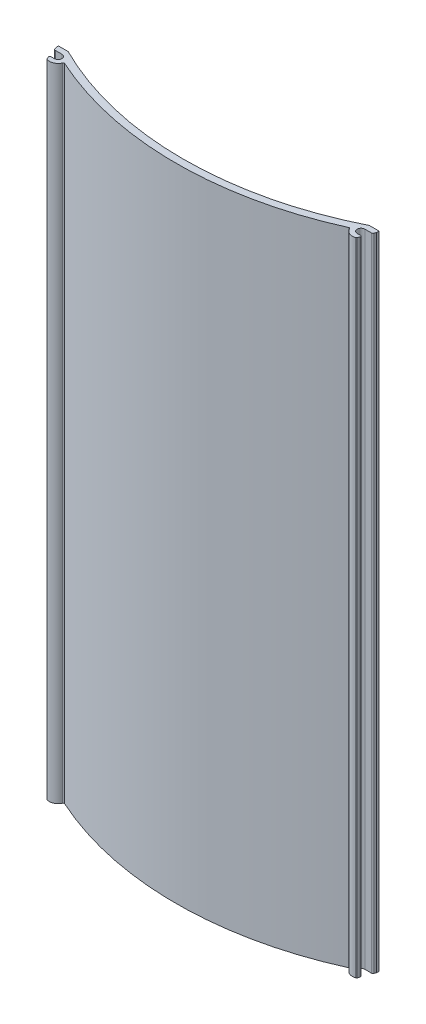
SolidWorks part; units mm, degrees
material "6463-T6"
ref_plane "Front Plane" through (0, 0, 0) normal (0, 0, 1) x (1, 0, 0)
ref_plane "Top Plane" through (0, 0, 0) normal (0, 1, 0) x (1, 0, 0)
ref_plane "Right Plane" through (0, 0, 0) normal (1, 0, 0) x (0, 0, -1)
sketch "Sketch1" plane through (0, 0, 0) normal (0, 1, 0) x (1, 0, 0)
  line L0 (0, 6.3541) -> (101.5848, 6.3541) construction
  line L1 (0, 0) -> (101.5848, 0) construction
  line L2 (0, 0) -> (0, 25.4) construction
  line L3 (0, 25.4) -> (101.5848, 25.4) construction
  line L4 (101.5848, 0) -> (101.5848, 25.4) construction
  line L5 (0, 12.7) -> (101.5848, 12.7) construction
  line L6 (0, 19.05) -> (101.5848, 19.05) construction
  line L7 (50.7924, 25.4) -> (50.7924, 0) construction
  line L8 (12.7, 25.4) -> (12.7, 0) construction
  line L9 (76.1924, 25.4) -> (76.1924, 0) construction
  line L10 (25.4, 25.4) -> (25.4, 0) construction
  line L11 (38.1, 25.4) -> (38.1, 0) construction
  line L12 (63.4924, 25.4) -> (63.4924, 0) construction
  line L13 (88.8924, 25.4) -> (88.8924, 0) construction
  line L15 (101.5848, 6.3541) -> (101.5848, 4.3221)
  line L16 (100.0608, 5.4351) -> (100.0608, 4.3221)
  line L17 (100.5688, 3.8141) -> (101.0768, 3.8141)
  line L19 (0, 0) -> (-3.2676, 0) construction
  line L20 (1.3386, 5.3381) -> (0, 5.3381)
  line L26 (90.0621, 10.016) -> (95.6249, 0.381)
  line L27 (95.6249, 0.381) -> (95.6249, 0)
  line L28 (95.6249, 0) -> (97.1489, 0)
  line L29 (97.1489, 0) -> (97.1489, 0.381)
  line L30 (97.1489, 0.381) -> (112.7608, 0.381)
  line L31 (112.7608, 0.381) -> (112.7608, 0)
  line L32 (112.7608, 0) -> (114.2848, 0)
  line L33 (114.2848, 0) -> (114.2848, 1.905)
  line L34 (114.2848, 1.905) -> (96.5048, 1.905)
  line L35 (96.5048, 1.905) -> (92.3687, 9.0689)
  line L36 (97.1489, 0.381) -> (95.6249, 0.381) construction
  line L38 (0, 5.3381) -> (0, 6.3541)
  line L39 (101.5848, 5.3381) -> (100.8228, 3.8141)
  arc A0 (101.5848, 6.3541) -> (0, 6.3541) centre (50.7924, -88.9) ccw
  arc A1 (100.0608, 5.4351) -> (1.3386, 5.3381) centre (50.7924, -88.9) ccw
  circle A2 centre (50.7924, -88.9) radius 107.95 construction
  circle A3 centre (50.7924, -88.9) radius 106.426 construction
  arc A4 (100.0608, 4.3221) -> (100.5688, 3.8141) centre (100.5688, 4.3221) ccw
  arc A5 (101.0768, 3.8141) -> (101.5848, 4.3221) centre (101.0768, 4.3221) ccw
  point P33 (100.0608, 3.8141)
  point P38 (101.5848, 3.8141)
  dimension "D12" = 2.54
  dimension "D14" = 0.508
  dimension "D16" = 107.95
  dimension "D1" = 101.5848
  dimension "D2" = 25.4
  dimension "D3" = 12.7
  dimension "D4" = 12.7
  dimension "D5" = 12.7
  dimension "D6" = 12.7
  dimension "D7" = 12.7
  dimension "D8" = 12.7
  dimension "D9" = 1.016
  dimension "D10" = 6.35
  dimension "D13" = 1.524
  dimension "D15" = 1.016
  dimension "D20" = 0.762
  dimension "D21" = 1.524
  dimension "D22" = 1.524
  dimension "D23" = 1.524
  dimension "D24" = 12.7
  dimension "D25" = 5.08
  dimension "D26" = 60
  dimension "D27" = 1.524
  dimension "D11" = 1.524
extrude "Boss-Extrude1" add sketch "Sketch1" along normal blind 203.2
sketch "Sketch3" plane through (0, 203.2, 0) normal (0, 1, 0) x (1, 0, 0)
  line L1 (101.5848, 6.3541) -> (101.5848, 5.3381) construction
  line L2 (100.0608, 2.9237) -> (101.5848, 2.9237)
  line L3 (101.5848, 2.9237) -> (101.5848, 5.5921)
  line L4 (101.5848, 5.5921) -> (100.0608, 5.4351)
  line L5 (100.0608, 5.4351) -> (100.0608, 2.9237)
  line L6 (0, 5.5921) -> (0.4068, 4.4744)
  line L7 (0, 5.3381) -> (0, 6.3541) construction
  line L8 (0.4068, 4.4744) -> (0, 4.4744)
  line L9 (0, 4.4744) -> (0, 5.5921)
  dimension "D1" = 0.762
  dimension "D2" = 0.762
  dimension "D3" = 2.6684
  dimension "D4" = 20
  dimension "D5" = 1.1176
extrude "Cut-Extrude1" cut sketch "Sketch3" against normal through all
sketch "Sketch2" plane through (0, 203.2, 0) normal (0, 1, 0) x (1, 0, 0)
  line L1 (101.5848, 6.3541) -> (101.5848, 5.5921) construction
  line L2 (101.2381, 4.6396) -> (101.5848, 5.5921)
  line L3 (101.2381, 4.6396) -> (98.7908, 4.6396)
  line L4 (98.7908, 2.2266) -> (99.8157, 2.2266)
  line L5 (100.1737, 1.7153) -> (99.9473, 1.0931)
  line L9 (50.7924, -88.9) -> (50.7924, 34.1205) construction
  line L10 (1.411, 1.7153) -> (1.6375, 1.0931)
  line L15 (2.794, 2.2266) -> (1.7691, 2.2266)
  line L16 (101.5848, 5.5921) -> (100.0608, 5.4351) construction
  line L19 (0.3467, 4.6396) -> (2.794, 4.6396)
  line L20 (0.3467, 4.6396) -> (0.0924, 5.3381)
  line L22 (101.5848, 5.5921) -> (100.0608, 5.4351)
  line L23 (1.3386, 5.3381) -> (0.0924, 5.3381) construction
  line L24 (1.3386, 5.3381) -> (0.0924, 5.3381)
  arc A0 (100.0608, 5.4351) -> (98.6476, 6.1598) centre (50.7924, -88.9) ccw
  arc A2 (98.7908, 2.2266) -> (98.7908, 4.6396) centre (98.7908, 3.4331) cw
  arc A3 (99.7187, 0.8651) -> (98.6476, 6.1598) centre (98.7908, 3.4331) cw
  arc A4 (99.8157, 2.2266) -> (100.1737, 1.7153) centre (99.8157, 1.8456) cw
  arc A5 (99.9473, 1.0931) -> (99.7187, 0.8651) centre (99.5892, 1.2234) cw
  arc A13 (1.6375, 1.0931) -> (1.866, 0.8651) centre (1.9955, 1.2234) ccw
  arc A14 (1.7691, 2.2266) -> (1.411, 1.7153) centre (1.7691, 1.8456) ccw
  arc A15 (1.866, 0.8651) -> (2.9371, 6.1598) centre (2.794, 3.4331) ccw
  arc A16 (2.794, 2.2266) -> (2.794, 4.6396) centre (2.794, 3.4331) ccw
  arc A17 (100.0608, 5.4351) -> (1.3386, 5.3381) centre (50.7924, -88.9) ccw construction
  arc A18 (2.9371, 6.1598) -> (1.3386, 5.3381) centre (50.7924, -88.9) ccw
  dimension "D2" = 2.413
  dimension "D3" = 5.461
  dimension "D4" = 0.381
  dimension "D12" = 20
  dimension "D6" = 2.794
  dimension "D5" = 0.9525
  dimension "D15" = 0.762
extrude "Boss-Extrude2" add sketch "Sketch2" against normal up to surface (203.2 mm away) up to face at (43.5213, 0, -9.2627)
fillet "Fillet1" radius 0.508 2 edges at (101.2381, 101.6, -4.6396) (0.3467, 101.6, -4.6396)
sketch "Sketch4" plane through (0, 203.2, 0) normal (0, 1, 0) x (1, 0, 0)
  line L10 (0, 5.5921) -> (0.225, 4.9738)
  line L11 (0.7024, 4.6396) -> (2.794, 4.6396)
  line L12 (2.794, 2.2266) -> (1.7691, 2.2266)
  line L13 (1.411, 1.7153) -> (1.6375, 1.0931)
  line L14 (99.9473, 1.0931) -> (100.1737, 1.7153)
  line L15 (99.8157, 2.2266) -> (98.7908, 2.2266)
  line L16 (98.7908, 4.6396) -> (100.8824, 4.6396)
  line L17 (101.3597, 4.9738) -> (101.5848, 5.5921)
  line L18 (101.5848, 5.5921) -> (101.5848, 6.3541)
  line L19 (0, 6.3541) -> (0, 5.5921)
  arc A0 (3.1857, 6.2846) -> (98.399, 6.2846) centre (50.7924, 101.753) ccw
  arc A1 (5.4194, 2.6829) -> (96.1653, 2.6829) centre (50.7924, 101.753) ccw
  arc A2 (98.6476, 6.1598) -> (99.7187, 0.8651) centre (98.7908, 3.4331) ccw construction
  arc A3 (98.6476, 6.1598) -> (2.9371, 6.1598) centre (50.7924, -88.9) ccw construction
  arc A4 (1.866, 0.8651) -> (2.9371, 6.1598) centre (2.794, 3.4331) ccw construction
  arc A5 (98.6476, 6.1598) -> (96.1653, 2.6829) centre (98.7908, 3.4331) ccw
  arc A6 (98.6476, 6.1598) -> (98.399, 6.2846) centre (50.7924, -88.9) ccw
  arc A7 (5.4194, 2.6829) -> (2.9371, 6.1598) centre (2.794, 3.4331) ccw
  arc A8 (3.1857, 6.2846) -> (2.9371, 6.1598) centre (50.7924, -88.9) ccw
  arc A14 (0.225, 4.9738) -> (0.7024, 4.6396) centre (0.7024, 5.1476) ccw
  arc A15 (2.794, 2.2266) -> (2.794, 4.6396) centre (2.794, 3.4331) ccw
  arc A16 (1.7691, 2.2266) -> (1.411, 1.7153) centre (1.7691, 1.8456) ccw
  arc A17 (1.6375, 1.0931) -> (1.866, 0.8651) centre (1.9955, 1.2234) ccw
  arc A18 (1.866, 0.8651) -> (2.9371, 6.1598) centre (2.794, 3.4331) ccw
  arc A20 (98.6476, 6.1598) -> (2.9371, 6.1598) centre (50.7924, -88.9) ccw
  arc A22 (98.6476, 6.1598) -> (99.7187, 0.8651) centre (98.7908, 3.4331) ccw
  arc A23 (99.7187, 0.8651) -> (99.9473, 1.0931) centre (99.5892, 1.2234) ccw
  arc A24 (100.1737, 1.7153) -> (99.8157, 2.2266) centre (99.8157, 1.8456) ccw
  arc A25 (98.7908, 4.6396) -> (98.7908, 2.2266) centre (98.7908, 3.4331) ccw
  arc A26 (100.8824, 4.6396) -> (101.3597, 4.9738) centre (100.8824, 5.1476) ccw
  arc A27 (101.5848, 6.3541) -> (0, 6.3541) centre (50.7924, -88.9) ccw
  arc A32 (5.4194, 2.6829) -> (3.9919, 5.8868) centre (2.794, 3.4331) ccw
  arc A36 (97.5929, 5.8868) -> (96.1653, 2.6829) centre (98.7908, 3.4331) ccw
  arc M35 (1.866, 0.8651) -> (2.9371, 6.1598) centre (2.794, 3.4331) ccw
  arc M37 (2.9371, 6.1598) -> (98.6476, 6.1598) centre (50.7924, -88.9) cw
  arc M39 (98.6476, 6.1598) -> (99.7187, 0.8651) centre (98.7908, 3.4331) ccw
  dimension "D2" = 213.36
  dimension "D3" = 108.966
  dimension "D1" = 0
extrude "Boss-Extrude3" add sketch "Sketch4" against normal through all contours A1 A0 M35 M39 | A0 M37 M35 | A0 M39 M37
sketch "Sketch5" plane through (0, 203.2, 0) normal (0, 1, 0) x (1, 0, 0)
  line L0 (101.5848, 6.3541) -> (98.5382, 6.3541)
  line L1 (3.0466, 6.3541) -> (0, 6.3541)
  line L10 (0, 5.5921) -> (0.225, 4.9738)
  line L11 (0.7024, 4.6396) -> (2.794, 4.6396)
  line L12 (2.794, 2.2266) -> (1.7691, 2.2266)
  line L13 (1.411, 1.7153) -> (1.6375, 1.0931)
  line L14 (99.9473, 1.0931) -> (100.1737, 1.7153)
  line L15 (99.8157, 2.2266) -> (98.7908, 2.2266)
  line L16 (98.7908, 4.6396) -> (100.8824, 4.6396)
  line L17 (101.3597, 4.9738) -> (101.5848, 5.5921)
  line L18 (101.5848, 5.5921) -> (101.5848, 6.3541)
  line L19 (0, 6.3541) -> (0, 5.5921)
  line L32 (99.9473, 1.0931) -> (100.1737, 1.7153)
  line L34 (99.8157, 2.2266) -> (98.7908, 2.2266)
  line L36 (98.7908, 4.6396) -> (100.8824, 4.6396)
  line L38 (101.3597, 4.9738) -> (101.5848, 5.5921)
  line L40 (101.5848, 5.5921) -> (101.5848, 6.3541)
  line L42 (0, 6.3541) -> (0, 5.5921)
  line L44 (0, 5.5921) -> (0.225, 4.9738)
  line L46 (0.7024, 4.6396) -> (2.794, 4.6396)
  line L48 (2.794, 2.2266) -> (1.7691, 2.2266)
  line L50 (1.411, 1.7153) -> (1.6375, 1.0931)
  arc A0 (98.399, 6.2846) -> (3.1857, 6.2846) centre (50.7924, -88.9) ccw construction
  arc A1 (3.1857, 6.2846) -> (98.399, 6.2846) centre (50.7924, 101.753) ccw construction
  arc A2 (98.399, 6.2846) -> (3.1857, 6.2846) centre (50.7924, -88.9) ccw
  arc A3 (3.0466, 6.3541) -> (3.1857, 6.2846) centre (50.7924, 101.753) ccw
  arc A4 (98.399, 6.2846) -> (98.5382, 6.3541) centre (50.7924, 101.753) ccw
  arc A6 (96.1653, 2.6829) -> (99.7187, 0.8651) centre (98.7908, 3.4331) ccw
  arc A7 (5.4194, 2.6829) -> (96.1653, 2.6829) centre (50.7924, 101.753) ccw
  arc A8 (1.866, 0.8651) -> (5.4194, 2.6829) centre (2.794, 3.4331) ccw
  arc A12 (0.225, 4.9738) -> (0.7024, 4.6396) centre (0.7024, 5.1476) ccw
  arc A13 (2.794, 2.2266) -> (2.794, 4.6396) centre (2.794, 3.4331) ccw
  arc A14 (1.7691, 2.2266) -> (1.411, 1.7153) centre (1.7691, 1.8456) ccw
  arc A15 (1.6375, 1.0931) -> (1.866, 0.8651) centre (1.9955, 1.2234) ccw
  arc A16 (1.866, 0.8651) -> (5.4194, 2.6829) centre (2.794, 3.4331) ccw
  arc A17 (5.4194, 2.6829) -> (96.1653, 2.6829) centre (50.7924, 101.753) ccw
  arc A18 (96.1653, 2.6829) -> (99.7187, 0.8651) centre (98.7908, 3.4331) ccw
  arc A19 (99.7187, 0.8651) -> (99.9473, 1.0931) centre (99.5892, 1.2234) ccw
  arc A20 (100.1737, 1.7153) -> (99.8157, 2.2266) centre (99.8157, 1.8456) ccw
  arc A21 (98.7908, 4.6396) -> (98.7908, 2.2266) centre (98.7908, 3.4331) ccw
  arc A22 (100.8824, 4.6396) -> (101.3597, 4.9738) centre (100.8824, 5.1476) ccw
  arc A23 (101.5848, 6.3541) -> (0, 6.3541) centre (50.7924, -88.9) ccw
  arc A35 (101.5848, 6.3541) -> (0, 6.3541) centre (50.7924, -88.9) ccw
  arc A47 (99.7187, 0.8651) -> (99.9473, 1.0931) centre (99.5892, 1.2234) ccw
  arc A49 (100.1737, 1.7153) -> (99.8157, 2.2266) centre (99.8157, 1.8456) ccw
  arc A51 (98.7908, 4.6396) -> (98.7908, 2.2266) centre (98.7908, 3.4331) ccw
  arc A53 (100.8824, 4.6396) -> (101.3597, 4.9738) centre (100.8824, 5.1476) ccw
  arc A55 (101.5848, 6.3541) -> (0, 6.3541) centre (50.7924, -88.9) ccw
  arc A56 (101.5848, 6.3541) -> (0, 6.3541) centre (50.7924, -88.9) ccw
  arc A57 (0.225, 4.9738) -> (0.7024, 4.6396) centre (0.7024, 5.1476) ccw
  arc A59 (2.794, 2.2266) -> (2.794, 4.6396) centre (2.794, 3.4331) ccw
  arc A61 (1.7691, 2.2266) -> (1.411, 1.7153) centre (1.7691, 1.8456) ccw
  arc A63 (1.6375, 1.0931) -> (1.866, 0.8651) centre (1.9955, 1.2234) ccw
  arc M35 (3.1857, 6.2846) -> (98.399, 6.2846) centre (50.7924, -88.9) cw
  arc M57 (101.5848, 6.3541) -> (0, 6.3541) centre (50.7924, -88.9) ccw
  dimension "D1" = 0
  dimension "D2" = 0
extrude "Cut-Extrude2" cut sketch "Sketch5" against normal through all contours A4 L0 L1 A3 M35 M57
fillet "Fillet2" radius 0.381 2 edges at (5.4194, 101.6, -2.6829) (96.1653, 101.6, -2.6829)
